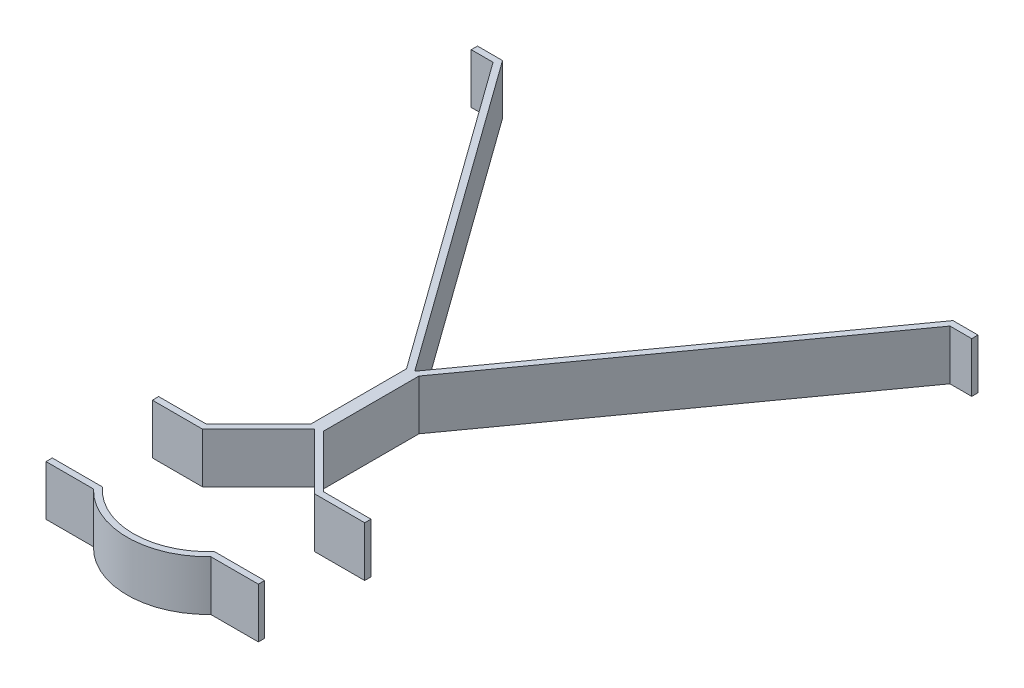
SolidWorks part; units mm, degrees
material "AISI 1020"
ref_plane "Front Plane" through (0, 0, 0) normal (0, 0, 1) x (1, 0, 0)
ref_plane "Top Plane" through (0, 0, 0) normal (0, 1, 0) x (1, 0, 0)
ref_plane "Right Plane" through (0, 0, 0) normal (1, 0, 0) x (0, 0, -1)
sketch "Sketch1" plane through (0, 0, 0) normal (0, 1, 0) x (1, 0, 0)
  line L0 (-127, 184.2435) -> (-114.3, 184.2435)
  line L1 (-114.3, 184.2435) -> (0, 25.4)
  line L2 (0, -25.4) -> (0, 25.4) construction
  line L3 (0, -25.4) -> (-28.4815, -53.8815)
  line L4 (-28.4815, -53.8815) -> (-53.8815, -53.8815)
  line L5 (0, -167.64) -> (0, 167.64) construction
  line L6 (28.4815, -53.8815) -> (53.8815, -53.8815)
  line L7 (0, -25.4) -> (28.4815, -53.8815)
  line L8 (114.3, 184.2435) -> (0, 25.4)
  line L9 (127, 184.2435) -> (114.3, 184.2435)
  line L10 (-53.8815, -104.6815) -> (-28.3981, -104.6815)
  line L11 (28.3981, -104.6815) -> (53.8815, -104.6815)
  line L12 (-127, 181.0685) -> (-115.9269, 181.0685)
  line L13 (-115.9269, 181.0685) -> (-3.175, 24.3764)
  line L14 (-3.175, -24.0849) -> (-29.7967, -50.7065)
  line L15 (-29.7967, -50.7065) -> (-53.8815, -50.7065)
  line L16 (-127, 184.2435) -> (-127, 181.0685)
  line L19 (-53.8815, -53.8815) -> (-53.8815, -50.7065)
  line L20 (-3.175, -24.0849) -> (-3.175, 24.3764)
  line L21 (3.175, -24.0849) -> (29.7967, -50.7065)
  line L22 (0, 25.4) -> (-3.175, 25.4)
  line L23 (29.7967, -50.7065) -> (53.8815, -50.7065)
  line L24 (-115.9269, 181.0685) -> (-2.5771, 23.5456) construction
  line L25 (-3.175, -25.4) -> (-3.175, 25.4) construction
  line L26 (-2.2451, -23.1549) -> (-29.7967, -50.7065) construction
  line L27 (127, 181.0685) -> (115.9269, 181.0685)
  line L28 (115.9269, 181.0685) -> (3.175, 24.3764)
  line L30 (53.8815, -53.8815) -> (53.8815, -50.7065)
  line L31 (127, 184.2435) -> (127, 181.0685)
  line L33 (3.175, -24.0849) -> (3.175, 24.3764)
  line L34 (-53.8815, -107.8565) -> (-29.7841, -107.8565)
  line L35 (29.7841, -107.8565) -> (53.8815, -107.8565)
  line L36 (115.9269, 181.0685) -> (2.5771, 23.5456) construction
  line L37 (3.175, -25.4) -> (3.175, 25.4) construction
  line L38 (2.2451, -23.1549) -> (29.7967, -50.7065) construction
  line L39 (-53.8815, -104.6815) -> (-53.8815, -107.8565)
  line L40 (53.8815, -104.6815) -> (53.8815, -107.8565)
  circle A0 centre (0, -79.2815) radius 38.1 construction
  arc A1 (-28.3981, -104.6815) -> (28.3981, -104.6815) centre (0, -79.2815) ccw
  arc A2 (-29.7841, -107.8565) -> (29.7841, -107.8565) centre (0, -79.2815) ccw
  point P10 (0, 0)
  point P15 (-120.65, 184.2435)
  point P16 (120.65, 184.2435)
  point P19 (0, 0)
  point P21 (96.4257, 184.2435)
  point P24 (72.6322, 184.2435)
  dimension "D2" = 76.2
  dimension "D1" = 241.3
  dimension "D3" = 263.525
  dimension "D4" = 90
  dimension "D5" = 50.8
  dimension "D6" = 25.4
  dimension "D7" = 25.4
  dimension "D8" = 50.8
  dimension "D9" = 12.7
  dimension "D10" = 3.175
  dimension "D11" = 3.175
  dimension "D12" = 3.175
  dimension "D13" = 3.175
  dimension "D14" = 3.175
extrude "Boss-Extrude1" add sketch "Sketch1" along normal mid plane 25.4
equation "\"A\"= 100"
equation "\"B\"= 100"
equation "\"C\"= 100"
equation "\"D\"= 100"
equation "\"E\"= 100"
